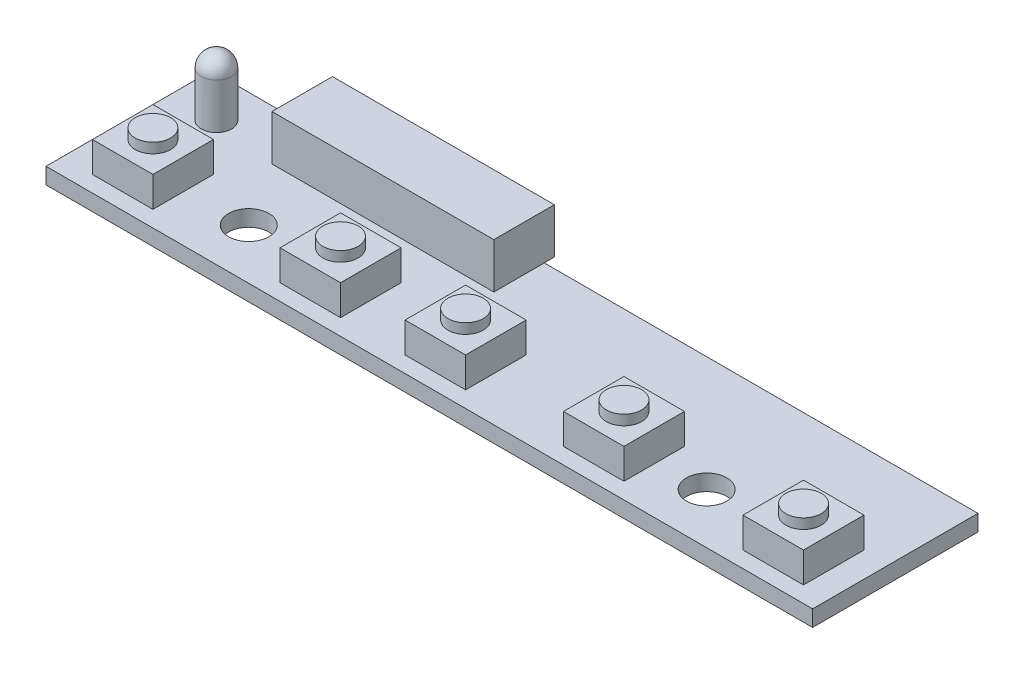
SolidWorks part; units mm, degrees
ref_plane "Płaszczyzna przednia" through (0, 0, 0) normal (0, 0, 1) x (1, 0, 0)
ref_plane "Płaszczyzna górna" through (0, 0, 0) normal (0, 1, 0) x (1, 0, 0)
ref_plane "Płaszczyzna prawa" through (0, 0, 0) normal (1, 0, 0) x (0, 0, -1)
sketch "Szkic1" plane through (0, 0, 0) normal (0, 1, 0) x (1, 0, 0)
  line L0 (-22.9, -3.2) -> (22.5, -3.2) construction
  line L1 (-38, -8.2) -> (38, -8.2)
  line L2 (-38, -8.2) -> (-38, 8.2)
  line L3 (-38, 8.2) -> (38, 8.2)
  line L4 (38, -8.2) -> (38, 8.2)
  line L5 (-38, -8.2) -> (38, 8.2) construction
  line L6 (-38, 8.2) -> (38, -8.2) construction
  circle A0 centre (-22.9, -3.2) radius 2
  circle A1 centre (22.5, -3.2) radius 2
  point P0 (0, 0)
  dimension "D3" = 49.4
  dimension "D4" = 4
  dimension "D7" = 5
  dimension "D1" = 16.4
  dimension "D2" = 76
  dimension "D5" = 13.1
  dimension "D6" = 13.5
extrude "Dodanie-wyciągnięcie1" add sketch "Szkic1" along normal blind 1.6
sketch "Szkic2" plane through (0, 1.6, 0) normal (0, 1, 0) x (1, 0, 0)
  line L0 (-38, -8.2) -> (38, -8.2) construction
  line L1 (-35, -6.6) -> (-29, -6.6)
  line L2 (-35, -6.6) -> (-35, -0.6)
  line L3 (-35, -0.6) -> (-29, -0.6)
  line L4 (-29, -6.6) -> (-29, -0.6)
  line L5 (-35, -6.6) -> (-29, -0.6) construction
  line L6 (-35, -0.6) -> (-29, -6.6) construction
  line L7 (-16.4, -6.6) -> (-10.4, -6.6)
  line L8 (-16.4, -6.6) -> (-16.4, -0.6)
  line L9 (-16.4, -0.6) -> (-10.4, -0.6)
  line L10 (-10.4, -6.6) -> (-10.4, -0.6)
  line L11 (-16.4, -6.6) -> (-10.4, -0.6) construction
  line L12 (-16.4, -0.6) -> (-10.4, -6.6) construction
  line L13 (-4, -6.6) -> (2, -6.6)
  line L14 (-4, -6.6) -> (-4, -0.6)
  line L15 (-4, -0.6) -> (2, -0.6)
  line L16 (2, -6.6) -> (2, -0.6)
  line L17 (-4, -6.6) -> (2, -0.6) construction
  line L18 (-4, -0.6) -> (2, -6.6) construction
  line L19 (11.7, -6.6) -> (17.7, -6.6)
  line L20 (11.7, -6.6) -> (11.7, -0.6)
  line L21 (11.7, -0.6) -> (17.7, -0.6)
  line L22 (17.7, -6.6) -> (17.7, -0.6)
  line L23 (11.7, -6.6) -> (17.7, -0.6) construction
  line L24 (11.7, -0.6) -> (17.7, -6.6) construction
  line L25 (29.5, -6.6) -> (35.5, -6.6)
  line L26 (29.5, -6.6) -> (29.5, -0.6)
  line L27 (29.5, -0.6) -> (35.5, -0.6)
  line L28 (35.5, -6.6) -> (35.5, -0.6)
  line L29 (29.5, -6.6) -> (35.5, -0.6) construction
  line L30 (29.5, -0.6) -> (35.5, -6.6) construction
  line L31 (-38, 8.2) -> (-38, -8.2) construction
  line L32 (38, -8.2) -> (38, 8.2) construction
  point P0 (-32, -3.6)
  point P5 (-13.4, -3.6)
  point P10 (-1, -3.6)
  point P15 (14.7, -3.6)
  point P20 (32.5, -3.6)
  point P27 (0, 0)
  dimension "D1" = 6
  dimension "D2" = 1.6
  dimension "D3" = 3
  dimension "D4" = 12.6
  dimension "D5" = 6.4
  dimension "D6" = 9.7
  dimension "D7" = 11.8
  dimension "D8" = 2.5
extrude "Dodanie-wyciągnięcie2" add sketch "Szkic2" along normal blind 3 contours L1 L4 L3 L2 | L7 L10 L9 L8 | L13 L16 L15 L14 | L19 L22 L21 L20 | L25 L28 L27 L26
sketch "Szkic3" plane through (0, 4.6, 0) normal (0, 1, 0) x (1, 0, 0)
  line L0 (-35, -6.6) -> (-35, -0.6) construction
  line L1 (-35, -0.6) -> (-29, -0.6) construction
  line L2 (-16.4, -0.6) -> (-10.4, -0.6) construction
  line L3 (-4, -0.6) -> (2, -0.6) construction
  line L4 (11.7, -0.6) -> (17.7, -0.6) construction
  line L5 (29.5, -0.6) -> (35.5, -0.6) construction
  circle A0 centre (-32, -3.6) radius 1.75
  circle A1 centre (-13.4, -3.6) radius 1.75
  circle A2 centre (-1, -3.6) radius 1.75
  circle A3 centre (14.7, -3.6) radius 1.75
  circle A4 centre (32.5, -3.6) radius 1.75
  point P4 (-13.5132, -3.6)
  point P9 (14.573, -3.6)
  point P12 (0, 0)
  point P15 (-35, -3.6)
  point P18 (-32, -0.6)
  point P21 (-13.4, -0.6)
  point P24 (-1, -0.6)
  point P25 (0, 0)
  point P28 (14.7, -0.6)
  point P31 (32.5, -0.6)
  dimension "D1" = 3.5
extrude "Dodanie-wyciągnięcie3" add sketch "Szkic3" along normal blind 1
sketch "Szkic4" plane through (0, 1.6, 0) normal (0, 1, 0) x (1, 0, 0)
  line L0 (-38, 8.2) -> (-38, -8.2) construction
  line L3 (38, 8.2) -> (-38, 8.2) construction
  circle A0 centre (-33.5, 4.2) radius 1.5
  dimension "D1" = 3
  dimension "D2" = 6
  dimension "D3" = 2.5
  dimension "D4" = 3
extrude "Dodanie-wyciągnięcie4" add sketch "Szkic4" along normal blind 6
fillet "Zaokrąglenie1" radius 1.5 1 edges at (-33.5, 7.6, -2.7)
sketch "Szkic5" plane through (0, 1.6, 0) normal (0, 1, 0) x (1, 0, 0)
  line L0 (38, 8.2) -> (-38, 8.2) construction
  line L1 (-27, 3.2) -> (-5, 3.2)
  line L2 (-27, 3.2) -> (-27, 9.2)
  line L3 (-27, 9.2) -> (-5, 9.2)
  line L4 (-5, 3.2) -> (-5, 9.2)
  line L5 (-38, 8.2) -> (-38, -8.2) construction
  dimension "D1" = 6
  dimension "D2" = 22
  dimension "D3" = 1
  dimension "D4" = 11
extrude "Dodanie-wyciągnięcie5" add sketch "Szkic5" along normal blind 4.5
